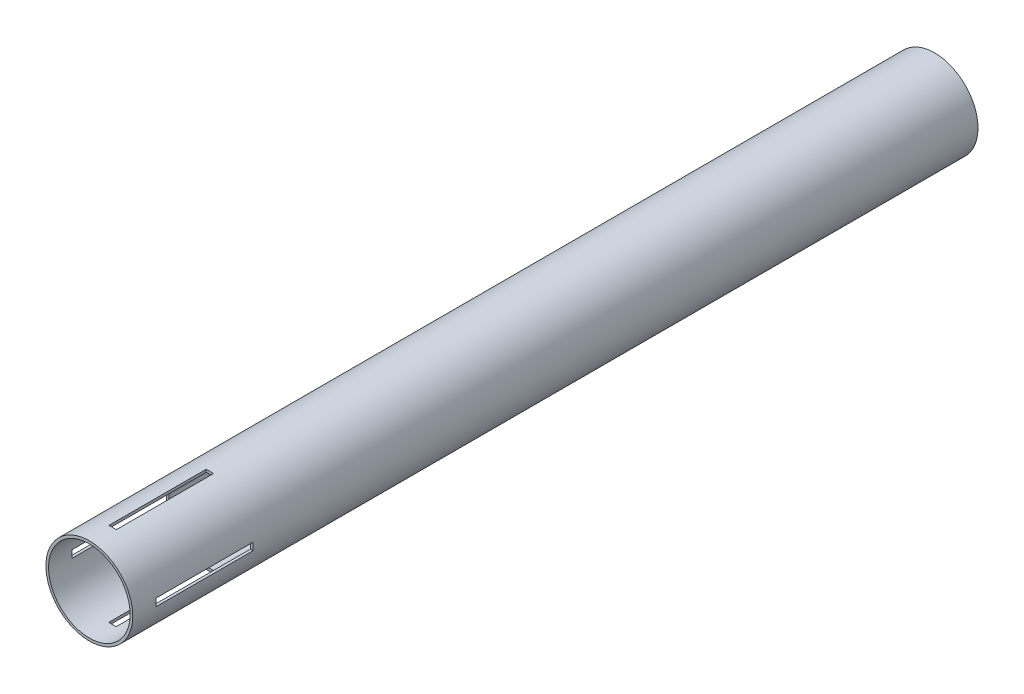
SolidWorks part; units mm, degrees
ref_plane "Front Plane" through (0, 0, 0) normal (0, 0, 1) x (1, 0, 0)
ref_plane "Top Plane" through (0, 0, 0) normal (0, 1, 0) x (1, 0, 0)
ref_plane "Right Plane" through (0, 0, 0) normal (1, 0, 0) x (0, 0, -1)
sketch "Sketch1" plane through (0, 0, 0) normal (0, 0, 1) x (1, 0, 0)
  circle A0 centre (0, 0) radius 20.555
  circle A1 centre (0, 0) radius 19.305
  dimension "D1" = 41.11
  dimension "D2" = 38.61
extrude "Boss-Extrude3" add sketch "Sketch1" against normal blind 400
sketch "Sketch2" plane through (0, 0, 0) normal (0, 1, 0) x (1, 0, 0)
  line L0 (0, -22.6105) -> (0, 22.6105) construction
  line L1 (-1.75, 57) -> (1.75, 57)
  line L2 (-1.75, 57) -> (-1.75, 11)
  line L3 (-1.75, 11) -> (1.75, 11)
  line L4 (1.75, 57) -> (1.75, 11)
  line L5 (-1.75, 57) -> (1.75, 11) construction
  line L6 (-1.75, 11) -> (1.75, 57) construction
  line L7 (-22.6105, 0) -> (22.6105, 0) construction
  point P0 (0, 34)
  dimension "D1" = 3.5
  dimension "D2" = 46
  dimension "D3" = 11
extrude "Cut-Extrude1" cut sketch "Sketch2" against normal through all both and the other way through all
pattern_circular "CirPattern1" count 2 over 90 about axis through (0, 0, -400) along (0, 0, 1) of "Cut-Extrude1"
sketch "Sketch3" [suppressed] plane through (0, 0, 0) normal (1, 0, 0) x (0, 0, -1)
  text T0 "STILL TESTING" font "Verdana Pro Cond" height in points 72
extrude "Cut-Extrude2" [suppressed] cut sketch "Sketch3" along normal through all
sketch "Sketch4" [suppressed] plane through (0, 0, -400) normal (0, 0, -1) x (-1, 0, 0)
  circle A0 centre (0, 0) radius 19.305
  circle A1 centre (0, 0) radius 20.455
  circle A2 centre (0, 0) radius 19.305 construction
  circle A3 centre (0, 0) radius 20.555 construction
  dimension "D1" = 0.1
extrude "Boss-Extrude4" [suppressed] add sketch "Sketch4" against normal up to surface (343 mm away)
